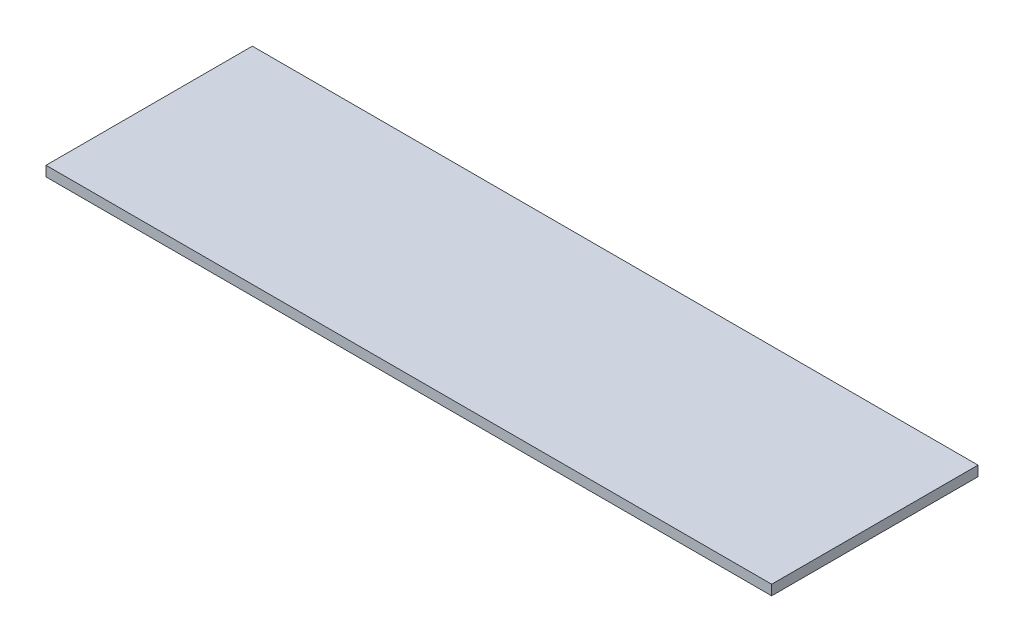
SolidWorks part; units mm, degrees
ref_plane "Front Plane" through (0, 0, 0) normal (0, 0, 1) x (1, 0, 0)
ref_plane "Top Plane" through (0, 0, 0) normal (0, 1, 0) x (1, 0, 0)
ref_plane "Right Plane" through (0, 0, 0) normal (1, 0, 0) x (0, 0, -1)
sketch "Sketch1" plane through (0, 0, 0) normal (0, 1, 0) x (1, 0, 0)
  line L1 (0, 0) -> (457.2, 0)
  line L2 (0, 0) -> (0, 130)
  line L3 (0, 130) -> (457.2, 130)
  line L4 (457.2, 0) -> (457.2, 130)
  dimension "D1" = 130
  dimension "D2" = 457.2
extrude "Boss-Extrude1" add sketch "Sketch1" along normal blind 6.35
